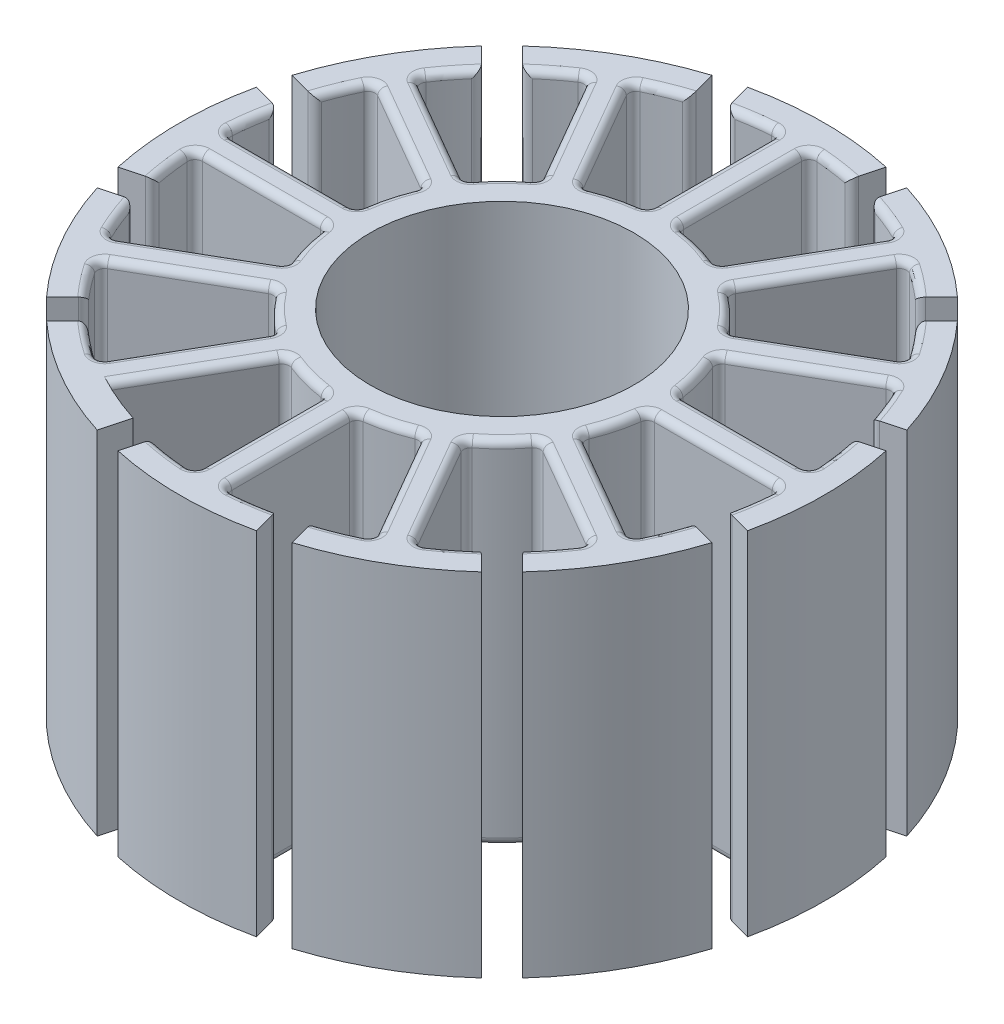
SolidWorks part; units mm, degrees
material "Plain Carbon Steel"
ref_plane "Front Plane" through (0, 0, 0) normal (0, 0, 1) x (1, 0, 0)
ref_plane "Top Plane" through (0, 0, 0) normal (0, 1, 0) x (1, 0, 0)
ref_plane "Right Plane" through (0, 0, 0) normal (1, 0, 0) x (0, 0, -1)
sketch "Sketch1" plane through (0, 0, 0) normal (0, 1, 0) x (1, 0, 0)
  line L0 (0, 0) -> (0, 11) construction
  line L1 (0, 0) -> (5.5, 9.5263) construction
  line L2 (0, 0) -> (9.5263, 5.5) construction
  line L3 (0, 0) -> (11, 0) construction
  line L4 (0, 0) -> (9.5263, -5.5) construction
  line L5 (0, 0) -> (5.5, -9.5263) construction
  line L6 (0, 0) -> (0, -11) construction
  line L7 (0, 0) -> (-5.5, -9.5263) construction
  line L8 (0, 0) -> (-9.5263, -5.5) construction
  line L9 (0, 0) -> (-11, 0) construction
  line L10 (0, 0) -> (-9.5263, 5.5) construction
  line L11 (0, 0) -> (-5.5, 9.5263) construction
  line L12 (-0.5, 9.9875) -> (-0.5, 5.4772)
  line L13 (0.5, 9.9875) -> (0.5, 5.4772)
  line L14 (5.4268, 8.3994) -> (3.1716, 4.4934)
  line L15 (4.5607, 8.8994) -> (2.3056, 4.9934)
  line L16 (8.8994, 4.5607) -> (4.9934, 2.3056)
  line L17 (8.3994, 5.4268) -> (4.4934, 3.1716)
  line L18 (9.9875, -0.5) -> (5.4772, -0.5)
  line L19 (9.9875, 0.5) -> (5.4772, 0.5)
  line L20 (8.3994, -5.4268) -> (4.4934, -3.1716)
  line L21 (8.8994, -4.5607) -> (4.9934, -2.3056)
  line L22 (4.5607, -8.8994) -> (2.3056, -4.9934)
  line L23 (5.4268, -8.3994) -> (3.1716, -4.4934)
  line L24 (-0.5, -9.9875) -> (-0.5, -5.4772)
  line L25 (0.5, -9.9875) -> (0.5, -5.4772)
  line L26 (-5.4268, -8.3994) -> (-3.1716, -4.4934)
  line L27 (-4.5607, -8.8994) -> (-2.3056, -4.9934)
  line L28 (-8.8994, -4.5607) -> (-4.9934, -2.3056)
  line L29 (-8.3994, -5.4268) -> (-4.4934, -3.1716)
  line L30 (-9.9875, 0.5) -> (-5.4772, 0.5)
  line L31 (-9.9875, -0.5) -> (-5.4772, -0.5)
  line L32 (-8.3994, 5.4268) -> (-4.4934, 3.1716)
  line L33 (-8.8994, 4.5607) -> (-4.9934, 2.3056)
  line L34 (-4.5607, 8.8994) -> (-2.3056, 4.9934)
  line L35 (-5.4268, 8.3994) -> (-3.1716, 4.4934)
  line L36 (0, 0) -> (-2.847, 10.6252) construction
  line L37 (0, 0) -> (2.847, 10.6252) construction
  line L38 (0, 0) -> (7.7782, 7.7782) construction
  line L39 (0, 0) -> (10.6252, 2.847) construction
  line L40 (0, 0) -> (10.6252, -2.847) construction
  line L41 (0, 0) -> (7.7782, -7.7782) construction
  line L42 (0, 0) -> (2.847, -10.6252) construction
  line L43 (0, 0) -> (-2.847, -10.6252) construction
  line L44 (0, 0) -> (-7.7782, -7.7782) construction
  line L45 (0, 0) -> (-10.6252, -2.847) construction
  line L46 (0, 0) -> (-10.6252, 2.847) construction
  line L47 (0, 0) -> (-7.7782, 7.7782) construction
  line L48 (-3.327, 10.4848) -> (-3.0679, 9.5178)
  line L49 (-2.3611, 10.7436) -> (-2.102, 9.7766)
  line L50 (3.327, 10.4848) -> (3.0679, 9.5178)
  line L51 (2.3611, 10.7436) -> (2.102, 9.7766)
  line L52 (8.1237, 7.4166) -> (7.4158, 6.7087)
  line L53 (7.4166, 8.1237) -> (6.7087, 7.4158)
  line L54 (10.7436, 2.3611) -> (9.7766, 2.102)
  line L55 (10.4848, 3.327) -> (9.5178, 3.0679)
  line L56 (10.4848, -3.327) -> (9.5178, -3.0679)
  line L57 (10.7436, -2.3611) -> (9.7766, -2.102)
  line L58 (7.4166, -8.1237) -> (6.7087, -7.4158)
  line L59 (8.1237, -7.4166) -> (7.4158, -6.7087)
  line L60 (2.3611, -10.7436) -> (2.102, -9.7766)
  line L61 (3.327, -10.4848) -> (3.0679, -9.5178)
  line L62 (-3.327, -10.4848) -> (-3.0679, -9.5178)
  line L63 (-2.3611, -10.7436) -> (-2.102, -9.7766)
  line L64 (-8.1237, -7.4166) -> (-7.4158, -6.7087)
  line L65 (-7.4166, -8.1237) -> (-6.7087, -7.4158)
  line L66 (-10.7436, -2.3611) -> (-9.7766, -2.102)
  line L67 (-10.4848, -3.327) -> (-9.5178, -3.0679)
  line L68 (-10.4848, 3.327) -> (-9.5178, 3.0679)
  line L69 (-10.7436, 2.3611) -> (-9.7766, 2.102)
  line L70 (-7.4166, 8.1237) -> (-6.7087, 7.4158)
  line L71 (-8.1237, 7.4166) -> (-7.4158, 6.7087)
  circle A0 centre (0, 0) radius 11
  circle A1 centre (0, 0) radius 4.5
  circle A2 centre (0, 0) radius 5.5
  circle A3 centre (0, 0) radius 10
  point P20 (0, 0)
  point P69 (0, 0)
  point P82 (0, 0)
  point P131 (0, 0)
  dimension "D1" = 22
  dimension "D2" = 9
  dimension "D3" = 11
  dimension "D4" = 20
  dimension "D6" = 1
  dimension "D8" = 15
  dimension "D10" = 1
  dimension "D5" = 12
  dimension "D7" = 12
  dimension "D9" = 12
  dimension "D11" = 12
extrude "Boss-Extrude1" add sketch "Sketch1" along normal blind 12 contours A2 A1 | L28 A3 L29 A2 | L30 A3 L31 A2 | L32 A3 L33 A2 | L34 A3 L35 A2 | L13 A3 L12 A2 | L14 A3 L15 A2 | L16 A3 L17 A2 | L18 A3 L19 A2 | L20 A3 L21 A2 | L22 A3 L23 A2 | L24 A3 L25 A2 | L26 A3 L27 A2 | A3 L65 A0 L62 | A3 L67 A0 L64 | A3 L69 A0 L66 | A3 L48 A0 L70 | A3 L71 A0 L68 | A3 L51 A0 L49 | A3 L53 A0 L50 | A3 L55 A0 L52 | A3 L57 A0 L54 | A3 L59 A0 L56 | A3 L61 A0 L58 | A3 L63 A0 L60
fillet "Fillet2" radius 0.25 188 edges at (0.5, 0, 7.7324) (0.5, 12, 7.7324) (3.4332, 0, 6.9464) (3.4332, 12, 6.9464) (-3.4332, 0, 6.9464) (-3.4332, 12, 6.9464) (-0.5, 0, 7.7324) (-0.5, 12, 7.7324) (-6.4464, 0, 4.2992) (-6.4464, 12, 4.2992) (-4.2992, 0, 6.4464) (-4.2992, 12, 6.4464) (-7.7324, 0, 0.5) (-7.7324, 12, 0.5) (-6.9464, 0, 3.4332) (-6.9464, 12, 3.4332) (-6.9464, 0, -3.4332) (-6.9464, 12, -3.4332) (-7.7324, 0, -0.5) (-7.7324, 12, -0.5) (-4.2992, 0, -6.4464) (-4.2992, 12, -6.4464) (-6.4464, 0, -4.2992) (-6.4464, 12, -4.2992) (-0.5, 0, -7.7324) (-0.5, 12, -7.7324) (-3.4332, 0, -6.9464) (-3.4332, 12, -6.9464) (3.4332, 0, -6.9464) (3.4332, 12, -6.9464) (0.5, 0, -7.7324) (0.5, 12, -7.7324) (6.4464, 0, -4.2992) (6.4464, 12, -4.2992) (4.2992, 0, -6.4464) (4.2992, 12, -6.4464) (7.7324, 0, -0.5) (7.7324, 12, -0.5) (6.9464, 0, -3.4332) (6.9464, 12, -3.4332) (6.9464, 0, 3.4332) (6.9464, 12, 3.4332) (7.7324, 0, 0.5) (7.7324, 12, 0.5) (4.2992, 0, 6.4464) (4.2992, 12, 6.4464) (6.4464, 0, 4.2992) (6.4464, 12, 4.2992) (0.5, 6, 5.4772) (1.4235, 12, 5.3126) (1.4235, 0, 5.3126) (2.3056, 6, 4.9934) (-2.3056, 6, 4.9934) (-1.4235, 12, 5.3126) (-1.4235, 0, 5.3126) (-0.5, 6, 5.4772) (-4.4934, 6, 3.1716) (-3.8891, 12, 3.8891) (-3.8891, 0, 3.8891) (-3.1716, 6, 4.4934) (-5.4772, 6, 0.5) (-5.3126, 12, 1.4235) (-5.3126, 0, 1.4235) (-4.9934, 6, 2.3056) (-4.9934, 6, -2.3056) (-5.3126, 12, -1.4235) (-5.3126, 0, -1.4235) (-5.4772, 6, -0.5) (-3.1716, 6, -4.4934) (-3.8891, 12, -3.8891) (-3.8891, 0, -3.8891) (-4.4934, 6, -3.1716) (-0.5, 6, -5.4772) (-1.4235, 12, -5.3126) (-1.4235, 0, -5.3126) (-2.3056, 6, -4.9934) (2.3056, 6, -4.9934) (1.4235, 12, -5.3126) (1.4235, 0, -5.3126) (0.5, 6, -5.4772) (4.4934, 6, -3.1716) (3.8891, 12, -3.8891) (3.8891, 0, -3.8891) (3.1716, 6, -4.4934) (5.4772, 6, -0.5) (5.3126, 12, -1.4235) (5.3126, 0, -1.4235) (4.9934, 6, -2.3056) (4.9934, 6, 2.3056) (5.3126, 12, 1.4235) (5.3126, 0, 1.4235) (5.4772, 6, 0.5) (3.1716, 6, 4.4934) (3.8891, 12, 3.8891) (3.8891, 0, 3.8891) (4.4934, 6, 3.1716) (8.8994, 6, -4.5607) (9.2388, 12, -3.8268) (9.2388, 0, -3.8268) (9.5178, 6, -3.0679) (7.4158, 6, -6.7087) (7.9335, 12, -6.0876) (7.9335, 0, -6.0876) (8.3994, 6, -5.4268) (5.4268, 6, -8.3994) (6.0876, 12, -7.9335) (6.0876, 0, -7.9335) (6.7087, 6, -7.4158) (3.0679, 6, -9.5178) (3.8268, 12, -9.2388) (3.8268, 0, -9.2388) (4.5607, 6, -8.8994) (0.5, 6, -9.9875) (1.3053, 12, -9.9144) (1.3053, 0, -9.9144) (2.102, 6, -9.7766) (-2.102, 6, -9.7766) (-1.3053, 12, -9.9144) (-1.3053, 0, -9.9144) (-0.5, 6, -9.9875) (-4.5607, 6, -8.8994) (-3.8268, 12, -9.2388) (-3.8268, 0, -9.2388) (-3.0679, 6, -9.5178) (-6.7087, 6, -7.4158) (-6.0876, 12, -7.9335) (-6.0876, 0, -7.9335) (-5.4268, 6, -8.3994) (-8.3994, 6, -5.4268) (-7.9335, 12, -6.0876) (-7.9335, 0, -6.0876) (-7.4158, 6, -6.7087) (-9.5178, 6, -3.0679) (-9.2388, 12, -3.8268) (-9.2388, 0, -3.8268) (-8.8994, 6, -4.5607) (-9.9875, 6, -0.5) (-9.9144, 12, -1.3053) (-9.9144, 0, -1.3053) (-9.7766, 6, -2.102) (-9.7766, 6, 2.102) (-9.9144, 12, 1.3053) (-9.9144, 0, 1.3053) (-9.9875, 6, 0.5) (-8.8994, 6, 4.5607) (-9.2388, 12, 3.8268) (-9.2388, 0, 3.8268) (-9.5178, 6, 3.0679) (-7.4158, 6, 6.7087) (-7.9335, 12, 6.0876) (-7.9335, 0, 6.0876) (-8.3994, 6, 5.4268) (-5.4268, 6, 8.3994) (-6.0876, 12, 7.9335) (-6.0876, 0, 7.9335) (-6.7087, 6, 7.4158) (-0.5, 6, 9.9875) (-1.3053, 12, 9.9144) (-1.3053, 0, 9.9144) (-2.102, 6, 9.7766) (2.102, 6, 9.7766) (1.3053, 12, 9.9144) (1.3053, 0, 9.9144) (0.5, 6, 9.9875) (9.7766, 6, -2.102) (9.9144, 12, -1.3053) (9.9144, 0, -1.3053) (9.9875, 6, -0.5) (9.9875, 6, 0.5) (9.9144, 12, 1.3053) (9.9144, 0, 1.3053) (9.7766, 6, 2.102) (9.5178, 6, 3.0679) (9.2388, 12, 3.8268) (9.2388, 0, 3.8268) (8.8994, 6, 4.5607) (8.3994, 6, 5.4268) (7.9335, 12, 6.0876) (7.9335, 0, 6.0876) (7.4158, 6, 6.7087) (6.7087, 6, 7.4158) (6.0876, 12, 7.9335) (6.0876, 0, 7.9335) (5.4268, 6, 8.3994) (4.5607, 6, 8.8994) (3.8268, 12, 9.2388) (3.8268, 0, 9.2388) (3.0679, 6, 9.5178)
